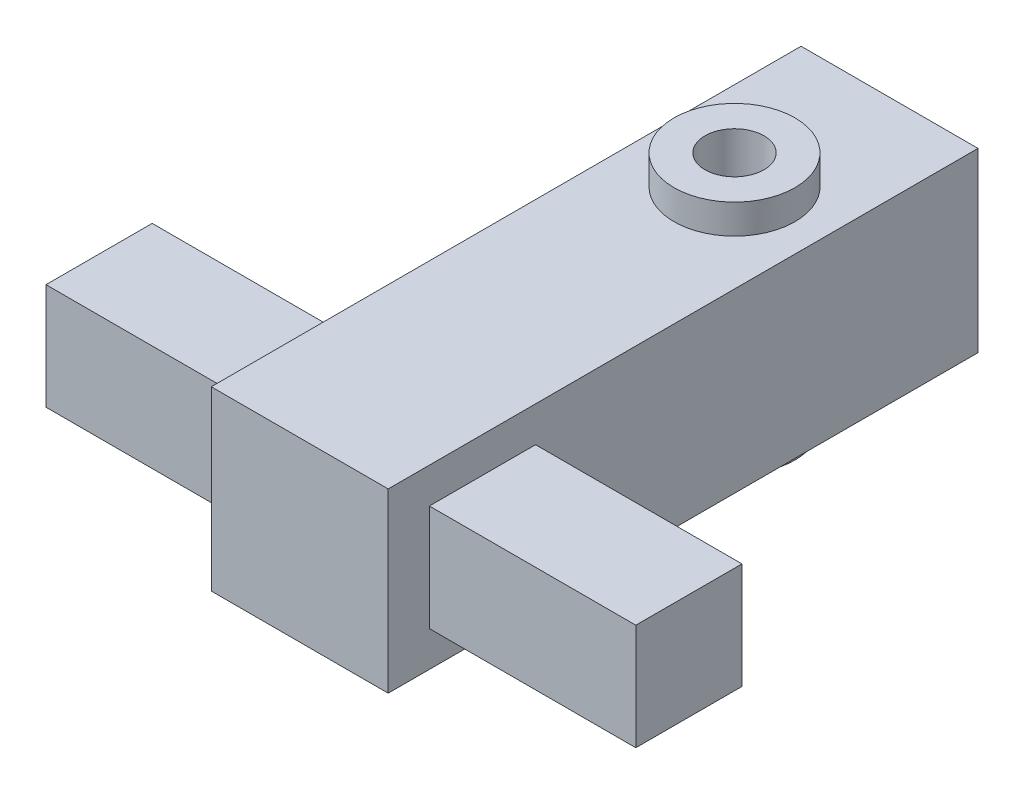
SolidWorks part; units mm, degrees
ref_plane "Front" through (0, 0, 0) normal (0, 0, 1) x (1, 0, 0)
ref_plane "Top" through (0, 0, 0) normal (0, 1, 0) x (1, 0, 0)
ref_plane "Right" through (0, 0, 0) normal (1, 0, 0) x (0, 0, -1)
sketch "草图2" plane through (0, 0, 0) normal (0, 0, 1) x (1, 0, 0)
  line L1 (-15, -15) -> (15, -15)
  line L2 (-15, -15) -> (-15, 15)
  line L3 (-15, 15) -> (15, 15)
  line L4 (15, -15) -> (15, 15)
  line L5 (-15, -15) -> (15, 15) construction
  line L6 (-15, 15) -> (15, -15) construction
  point P0 (0, 0)
  dimension "D1" = 30
  dimension "D2" = 30
extrude "凸台-拉伸1" add sketch "草图2" along normal blind 100
sketch "草图3" plane through (15, 0, 0) normal (1, 0, 0) x (0, 0, -1)
  line L1 (-75.019, 9) -> (-93.019, 9)
  line L2 (-75.019, 9) -> (-75.019, -9)
  line L3 (-75.019, -9) -> (-93.019, -9)
  line L4 (-93.019, 9) -> (-93.019, -9)
  line L5 (-75.019, 9) -> (-93.019, -9) construction
  line L6 (-75.019, -9) -> (-93.019, 9) construction
  point P0 (-84.019, 0)
  dimension "D1" = 18
  dimension "D2" = 18
extrude "凸台-拉伸2" add sketch "草图3" along normal blind 35
pattern_circular "阵列(圆周)1" count 2 over 360 about axis through (0, 0, 0) along (0, 0, 1) of "凸台-拉伸2"
sketch "草图4" plane through (0, 15, 0) normal (0, 1, 0) x (1, 0, 0)
  circle A0 centre (0, -26.2854) radius 10.2542
  circle A1 centre (0, -26.2854) radius 5.2542
  dimension "D1" = 20.5085
  dimension "D2" = 5
extrude "凸台-拉伸4" add sketch "草图4" along normal blind 5 contours A0
sketch "草图5" plane through (0, 20, 0) normal (0, 1, 0) x (1, 0, 0)
  circle A0 centre (0, -26.2854) radius 5
extrude "切除-拉伸2" cut sketch "草图5" against normal blind 15
pattern_circular "阵列(圆周)3" count 2 over 360 about axis through (0, 0, 100) along (0, 0, -1) of "凸台-拉伸4"
pattern_circular "阵列(圆周)4" count 2 over 360 about axis through (0, 0, 100) along (0, 0, -1) of "切除-拉伸2"
